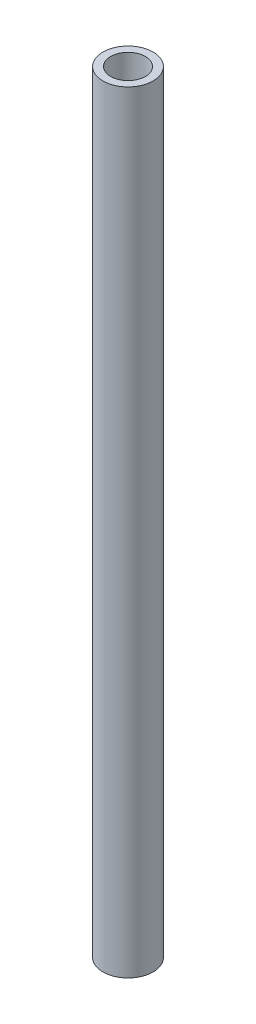
SolidWorks part; units mm, degrees
ref_plane "Спереди" through (0, 0, 0) normal (0, 0, 1) x (1, 0, 0)
ref_plane "Сверху" through (0, 0, 0) normal (0, 1, 0) x (1, 0, 0)
ref_plane "Справа" through (0, 0, 0) normal (1, 0, 0) x (0, 0, -1)
sketch "Эскиз1" plane through (0, 0, 0) normal (0, 1, 0) x (1, 0, 0)
  circle A0 centre (0, 0) radius 4.5
extrude "Вытянуть-Тонкостенный1" add sketch "Эскиз1" along normal blind 200 thin
